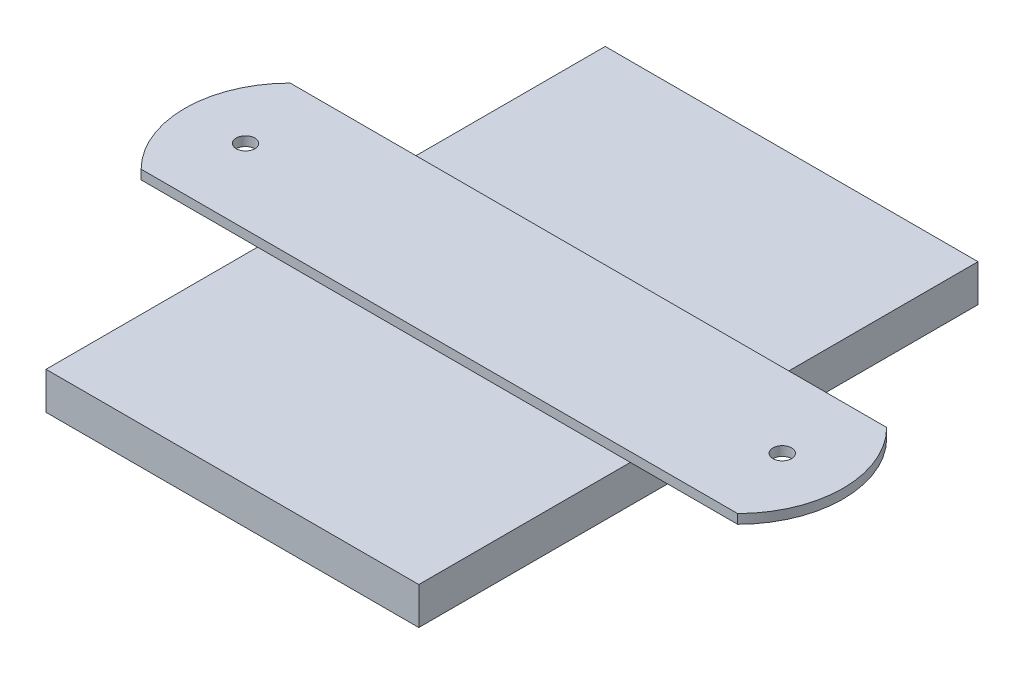
SolidWorks part; units mm, degrees
ref_plane "Front Plane" through (0, 0, 0) normal (0, 0, 1) x (1, 0, 0)
ref_plane "Top Plane" through (0, 0, 0) normal (0, 1, 0) x (1, 0, 0)
ref_plane "Right Plane" through (0, 0, 0) normal (1, 0, 0) x (0, 0, -1)
sketch "Sketch1" plane through (0, 0, 0) normal (0, 1, 0) x (1, 0, 0)
  line L1 (0, 0) -> (63.5, 0)
  line L2 (0, 0) -> (0, 95.25)
  line L3 (0, 95.25) -> (63.5, 95.25)
  line L4 (63.5, 0) -> (63.5, 95.25)
extrude "Boss-Extrude1" add sketch "Sketch1" along normal mid plane 6.35
sketch "Sketch2" plane through (0, 3.175, 0) normal (0, 1, 0) x (1, 0, 0)
  line L0 (30.9686, 61.4325) -> (30.9686, 36.0325) construction
  line L1 (-19.8314, 36.0325) -> (81.7686, 36.0325)
  line L2 (-19.8314, 36.0325) -> (-19.8314, 61.4325)
  line L3 (-19.8314, 61.4325) -> (81.7686, 61.4325)
  line L4 (81.7686, 36.0325) -> (81.7686, 61.4325)
  line L5 (-19.8314, 36.0325) -> (81.7686, 61.4325) construction
  line L6 (-19.8314, 61.4325) -> (81.7686, 36.0325) construction
  arc A0 (-19.8314, 36.0325) -> (-19.8314, 61.4325) centre (-7.1314, 48.7325) cw
  arc A1 (81.7686, 61.4325) -> (81.7686, 36.0325) centre (69.0686, 48.7325) cw
  circle A2 centre (-14.7437, 48.7325) radius 1.5875
  circle A3 centre (76.6809, 48.7325) radius 1.5875
  point P0 (30.9686, 48.7325)
  line M5 (0, 95.25) -> (0, 0)
  line M7 (63.5, 0) -> (63.5, 95.25)
extrude "Boss-Extrude2" add sketch "Sketch2" along normal blind 1.5875 contours L3 L1 M5 M7 | L3 L2 L1 M5 | L1 L4 L3 M7 | A0 L2 | A1 L4
